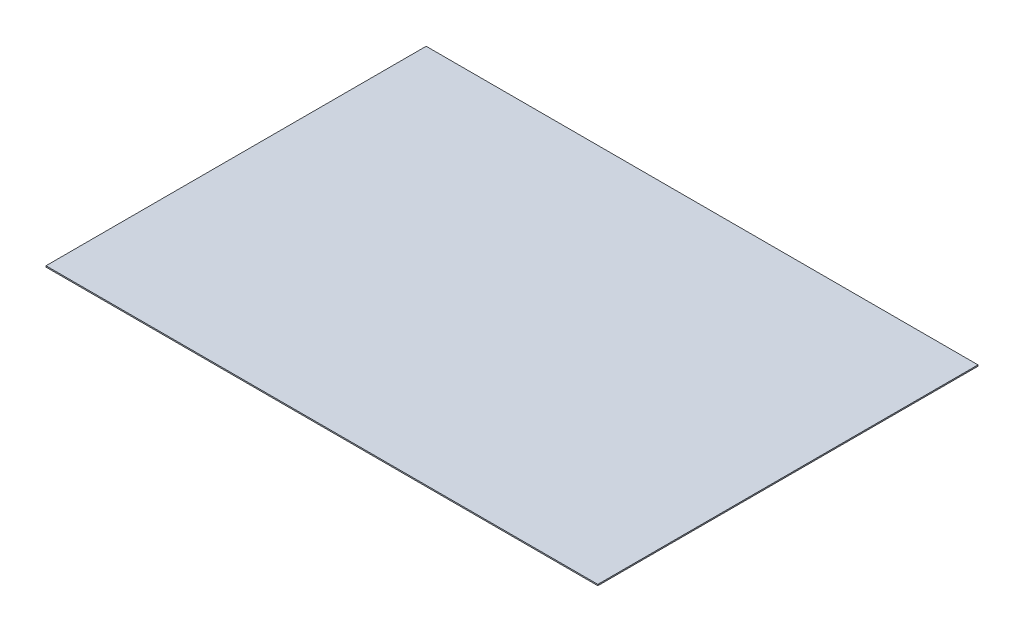
SolidWorks part; units mm, degrees
ref_plane "Front Plane" through (0, 0, 0) normal (0, 0, 1) x (1, 0, 0)
ref_plane "Top Plane" through (0, 0, 0) normal (0, 1, 0) x (1, 0, 0)
ref_plane "Right Plane" through (0, 0, 0) normal (1, 0, 0) x (0, 0, -1)
sketch "Sketch1" plane through (0, 0, 0) normal (0, 1, 0) x (1, 0, 0)
  line L1 (-225, 155) -> (225, 155)
  line L2 (-225, 155) -> (-225, -155)
  line L3 (-225, -155) -> (225, -155)
  line L4 (225, 155) -> (225, -155)
  line L5 (-225, 155) -> (225, -155) construction
  line L6 (-225, -155) -> (225, 155) construction
  point P0 (0, 0)
  dimension "D1" = 450
  dimension "D2" = 310
extrude "Boss-Extrude1" add sketch "Sketch1" along normal blind 1
